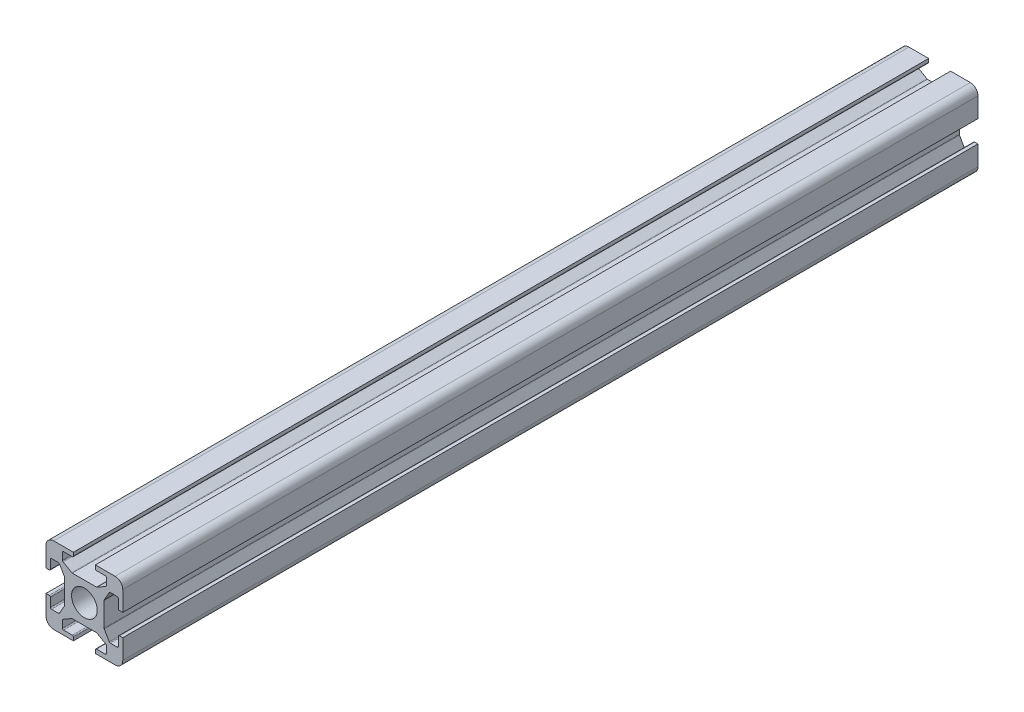
SolidWorks part; units mm, degrees
material "6061-T6 (SS)"
ref_plane "Alzado" through (0, 0, 0) normal (0, 0, 1) x (1, 0, 0)
ref_plane "Planta" through (0, 0, 0) normal (0, 1, 0) x (1, 0, 0)
ref_plane "Vista lateral" through (0, 0, 0) normal (1, 0, 0) x (0, 0, -1)
sketch "Croquis1" plane through (0, 0, 0) normal (0, 0, 1) x (1, 0, 0)
  line L0 (-10, 0) -> (10, 0) construction
  line L1 (0, 32.431) -> (0, -32.431) construction
  line L2 (-17.5, -5) -> (-16, -5)
  line L3 (-15.5, -15.5) -> (15.5, -15.5) construction
  line L4 (-15.5, -15.5) -> (-15.5, 15.5) construction
  line L5 (17.5, -17.5) -> (17.5, 17.5) construction
  line L6 (-17.5, -17.5) -> (17.5, 17.5) construction
  line L7 (-17.5, 17.5) -> (17.5, -17.5) construction
  line L8 (9, -9) -> (-9, -9) construction
  line L9 (9, -9) -> (9, 9) construction
  line L10 (9, 9) -> (-9, 9) construction
  line L11 (-9, -9) -> (-9, 9) construction
  line L12 (9, -9) -> (-9, 9) construction
  line L13 (9, 9) -> (-9, -9) construction
  line L14 (-15.5, 15.5) -> (15.5, 15.5) construction
  line L15 (15.5, -15.5) -> (15.5, 15.5) construction
  line L16 (-15.5, -15.5) -> (15.5, 15.5) construction
  line L17 (-15.5, 15.5) -> (15.5, -15.5) construction
  line L18 (-14.0807, -14.0828) -> (13.915, 13.9172) construction
  line L19 (-9, 15.5) -> (9, 15.5)
  line L20 (-15.5, -5.5) -> (-15.5, -9.5)
  line L21 (-15, -10) -> (-11.7901, -10)
  line L22 (-11.356, -9.7481) -> (-9.0659, -5.7407)
  line L23 (-9, -5.4926) -> (-9, 5.4926)
  line L24 (-11.356, 9.7481) -> (-9.0659, 5.7407)
  line L25 (-15, 10) -> (-11.7901, 10)
  line L26 (-15.5, 5.5) -> (-15.5, 9.5)
  line L27 (-17.5, 5) -> (-16, 5)
  line L28 (-17.5, 14) -> (-17.5, 5)
  line L29 (-17.5, -5) -> (-17.5, -14)
  line L30 (5, 17.5) -> (5, 16)
  line L31 (-17.5, 17.5) -> (17.5, 17.5) construction
  line L32 (5.5, 15.5) -> (9.5, 15.5)
  line L33 (10, 15) -> (10, 11.7901)
  line L34 (-17.5, -17.5) -> (17.5, -17.5) construction
  line L35 (9.7481, 11.356) -> (5.7407, 9.0659)
  line L36 (-17.5, -17.5) -> (-17.5, 17.5) construction
  line L37 (-17.5, 17.5) -> (17.5, 17.5) construction
  line L38 (17.5, -17.5) -> (17.5, 17.5) construction
  line L39 (-17.5, -17.5) -> (17.5, 17.5) construction
  line L40 (-17.5, 17.5) -> (17.5, -17.5) construction
  line L41 (-5.4926, 9) -> (5.4926, 9)
  line L42 (-9.7481, 11.356) -> (-5.7407, 9.0659)
  line L43 (-10, 15) -> (-10, 11.7901)
  line L44 (-10, -10) -> (10, 10) construction
  line L45 (-10, 10) -> (10, -10) construction
  line L46 (-5.5, 15.5) -> (-9.5, 15.5)
  line L47 (-5, 17.5) -> (-5, 16)
  line L48 (-14, -14) -> (14, 14) construction
  line L49 (-14, 14) -> (14, -14) construction
  line L50 (17.5, -5) -> (16, -5)
  line L51 (15.5, -5.5) -> (15.5, -9.5)
  line L52 (15, -10) -> (11.7901, -10)
  line L53 (11.356, -9.7481) -> (9.0659, -5.7407)
  line L54 (9, 5.4926) -> (9, -5.4926)
  line L55 (11.356, 9.7481) -> (9.0659, 5.7407)
  line L56 (15, 10) -> (11.7901, 10)
  line L57 (15.5, 5.5) -> (15.5, 9.5)
  line L58 (17.5, 5) -> (16, 5)
  line L59 (-5, -17.5) -> (-5, -16)
  line L60 (-5.5, -15.5) -> (-9.5, -15.5)
  line L61 (-10, -15) -> (-10, -11.7901)
  line L62 (-9.7481, -11.356) -> (-5.7407, -9.0659)
  line L63 (5.4926, -9) -> (-5.4926, -9)
  line L64 (9.7481, -11.356) -> (5.7407, -9.0659)
  line L65 (10, -15) -> (10, -11.7901)
  line L66 (5.5, -15.5) -> (9.5, -15.5)
  line L67 (5, -17.5) -> (5, -16)
  line L68 (-5, 17.5) -> (-14, 17.5)
  line L69 (5, 17.5) -> (14, 17.5)
  line L70 (17.5, 14) -> (17.5, 5)
  line L71 (17.5, -5) -> (17.5, -14)
  line L72 (14, -17.5) -> (5, -17.5)
  line L73 (-14, -17.5) -> (-5, -17.5)
  circle A0 centre (0, 0) radius 5.85
  arc A1 (-9.0659, -5.7407) -> (-9, -5.4926) centre (-9.5, -5.4926) ccw
  arc A2 (-11.7901, -10) -> (-11.356, -9.7481) centre (-11.7901, -9.5) ccw
  arc A3 (-15.5, -9.5) -> (-15, -10) centre (-15, -9.5) ccw
  arc A4 (-16, -5) -> (-15.5, -5.5) centre (-16, -5.5) cw
  arc A5 (-11.7901, 10) -> (-11.356, 9.7481) centre (-11.7901, 9.5) cw
  arc A6 (-15.5, 9.5) -> (-15, 10) centre (-15, 9.5) cw
  arc A7 (-16, 5) -> (-15.5, 5.5) centre (-16, 5.5) ccw
  arc A8 (-9.0659, 5.7407) -> (-9, 5.4926) centre (-9.5, 5.4926) cw
  arc A9 (5, 16) -> (5.5, 15.5) centre (5.5, 16) ccw
  arc A10 (9.5, 15.5) -> (10, 15) centre (9.5, 15) cw
  arc A11 (10, 11.7901) -> (9.7481, 11.356) centre (9.5, 11.7901) cw
  arc A12 (5.7407, 9.0659) -> (5.4926, 9) centre (5.4926, 9.5) cw
  arc A13 (-5.7407, 9.0659) -> (-5.4926, 9) centre (-5.4926, 9.5) ccw
  arc A14 (-10, 11.7901) -> (-9.7481, 11.356) centre (-9.5, 11.7901) ccw
  arc A15 (-9.5, 15.5) -> (-10, 15) centre (-9.5, 15) ccw
  arc A16 (-5, 16) -> (-5.5, 15.5) centre (-5.5, 16) cw
  arc A17 (16, -5) -> (15.5, -5.5) centre (16, -5.5) ccw
  arc A18 (15.5, -9.5) -> (15, -10) centre (15, -9.5) cw
  arc A19 (11.7901, -10) -> (11.356, -9.7481) centre (11.7901, -9.5) cw
  arc A20 (9.0659, -5.7407) -> (9, -5.4926) centre (9.5, -5.4926) cw
  arc A21 (9.0659, 5.7407) -> (9, 5.4926) centre (9.5, 5.4926) ccw
  arc A22 (11.7901, 10) -> (11.356, 9.7481) centre (11.7901, 9.5) ccw
  arc A23 (15.5, 9.5) -> (15, 10) centre (15, 9.5) ccw
  arc A24 (16, 5) -> (15.5, 5.5) centre (16, 5.5) cw
  arc A25 (-5, -16) -> (-5.5, -15.5) centre (-5.5, -16) ccw
  arc A26 (-9.5, -15.5) -> (-10, -15) centre (-9.5, -15) cw
  arc A27 (-10, -11.7901) -> (-9.7481, -11.356) centre (-9.5, -11.7901) cw
  arc A28 (-5.7407, -9.0659) -> (-5.4926, -9) centre (-5.4926, -9.5) cw
  arc A29 (5.7407, -9.0659) -> (5.4926, -9) centre (5.4926, -9.5) ccw
  arc A30 (10, -11.7901) -> (9.7481, -11.356) centre (9.5, -11.7901) ccw
  arc A31 (9.5, -15.5) -> (10, -15) centre (9.5, -15) ccw
  arc A32 (5, -16) -> (5.5, -15.5) centre (5.5, -16) cw
  arc A33 (17.5, -14) -> (14, -17.5) centre (14, -14) cw
  arc A34 (14, 17.5) -> (17.5, 14) centre (14, 14) cw
  arc A35 (-14, 17.5) -> (-17.5, 14) centre (-14, 14) ccw
  arc A36 (-17.5, -14) -> (-14, -17.5) centre (-14, -14) ccw
  point P0 (0, 0)
  point P4 (0, 0)
  point P31 (0, 0)
  point P37 (-11.5, -10)
  point P48 (-15.5, -10)
  point P50 (0, -15.5)
  point P53 (-9, 0)
  point P56 (0, 15.5172)
  point P149 (0, 0)
  dimension "D3" = 11.7
  dimension "D11" = 0.5
  dimension "D12" = 4
  dimension "D13" = 3.5
  dimension "D14" = 3.5
  dimension "D1" = 35
  dimension "D2" = 35
  dimension "D4" = 18
  dimension "D5" = 18
  dimension "D6" = 31
  dimension "D7" = 10
  dimension "D8" = 20
  dimension "D9" = 4
  dimension "D10" = 35
extrude "Saliente-Extruir1" add sketch "Croquis1" along normal blind 390 contours L29 A36 L73 L59 A25 L60 A26 L61 A27 L62 A28 L63 A29 L64 A30 L65 A31 L66 A32 L67 L72 A33 L71 L50 A17 L51 A18 L52 A19 L53 A20 L54 A21 L55 A22 L56 A23 L57 A24 L58 L70 A34 L69 L30 A9 L19 L32 A10 L33 A11 L35
